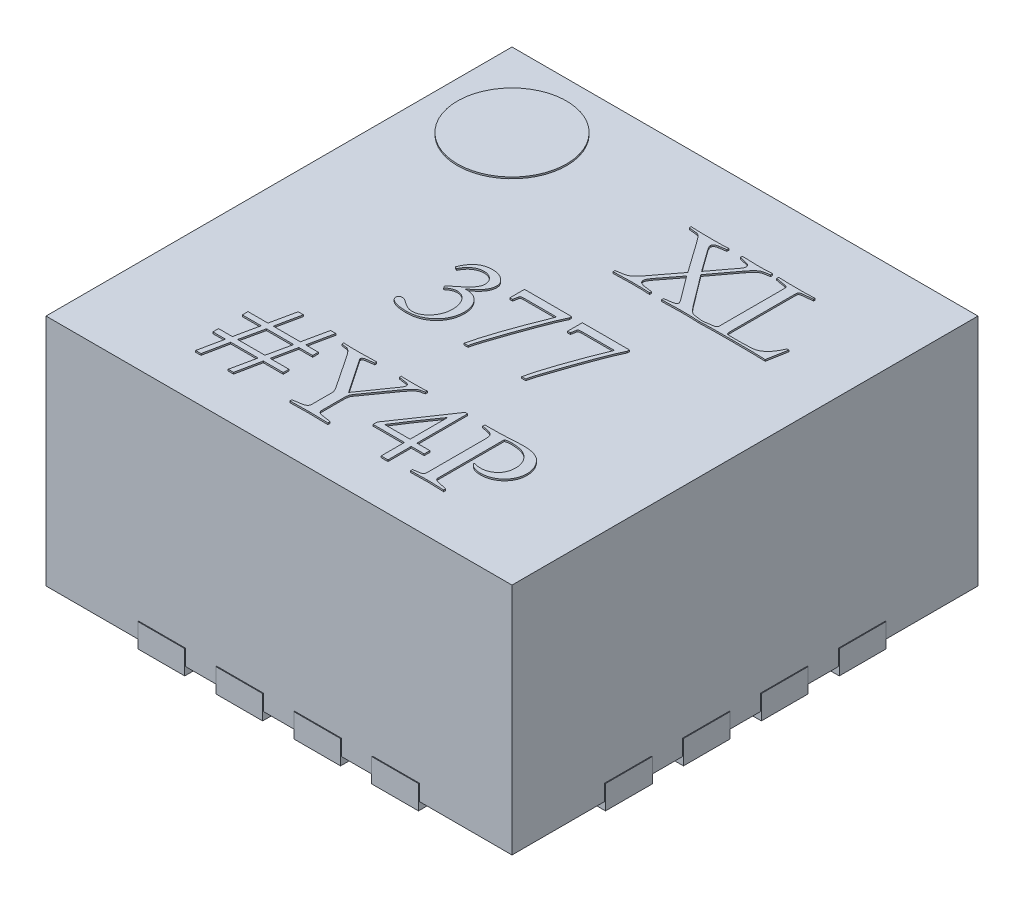
SolidWorks part; units mm, degrees
ref_plane "前视基准面" through (0, 0, 0) normal (0, 0, 1) x (1, 0, 0)
ref_plane "上视基准面" through (0, 0, 0) normal (0, 1, 0) x (1, 0, 0)
ref_plane "右视基准面" through (0, 0, 0) normal (1, 0, 0) x (0, 0, -1)
sketch "俯视" plane through (0, 0, 0) normal (0, 1, 0) x (1, 0, 0)
  line L1 (-1.495, 1.495) -> (1.495, 1.495)
  line L2 (-1.495, 1.495) -> (-1.495, -1.495)
  line L3 (-1.495, -1.495) -> (1.495, -1.495)
  line L4 (1.495, 1.495) -> (1.495, -1.495)
  line L5 (-1.495, 1.495) -> (1.495, -1.495) construction
  line L6 (-1.495, -1.495) -> (1.495, 1.495) construction
  point P0 (0, 0)
  dimension "D1" = 2.99
  dimension "D2" = 1.495
extrude "凸台-拉伸1" add sketch "俯视" against normal blind 1.5
ref_plane "基准面1" through (0, -1.55, 0) normal (0, 1, 0) x (1, 0, 0)
sketch "焊盘视图" plane through (0, -1.55, 0) normal (0, 1, 0) x (1, 0, 0)
  line L0 (0, 2) -> (0, -2) construction
  line L1 (-2, 0) -> (2, 0) construction
  line L2 (-1.5, 1.5) -> (1.5, 1.5) construction
  line L3 (-1.5, 1.5) -> (-1.5, -1.5) construction
  line L4 (-1.5, -1.5) -> (1.5, -1.5) construction
  line L5 (1.5, -1.5) -> (1.5, 1.5) construction
  line L6 (0.1, 1.5) -> (0.1, 1.25)
  line L7 (0.25, 2) -> (0.25, 1.3) construction
  line L8 (0.4, 1.5) -> (0.4, 1.25)
  line L10 (-0.25, 2) -> (-0.25, 1.3) construction
  line L11 (-0.75, 2) -> (-0.75, 1.3) construction
  line L12 (-2, -0.25) -> (-1.1693, -0.25) construction
  line L13 (-2, -0.75) -> (-1.1693, -0.75) construction
  line L14 (-2, 0.25) -> (-1.1693, 0.25) construction
  line L15 (-2, 0.75) -> (-1.1693, 0.75) construction
  line L16 (0.25, -2) -> (0.25, -1.1582) construction
  line L17 (-0.25, -2) -> (-0.25, -1.1275) construction
  line L18 (0.75, -2) -> (0.75, -1.1582) construction
  line L19 (-0.75, -2) -> (-0.75, -1.1275) construction
  line L20 (1.118, -0.75) -> (2, -0.75) construction
  line L21 (1.118, -0.25) -> (2, -0.25) construction
  line L22 (1.118, 0.25) -> (2, 0.25) construction
  line L23 (1.118, 0.75) -> (2, 0.75) construction
  line L24 (0.75, 1.3) -> (0.75, 2) construction
  line L25 (0.4, 1.5) -> (0.1, 1.5)
  line L26 (-0.4, 1.5) -> (-0.4, 1.25)
  line L27 (-0.1, 1.5) -> (-0.1, 1.25)
  line L28 (-0.1, 1.5) -> (-0.4, 1.5)
  line L29 (-0.6, -1.5) -> (-0.6, -1.25)
  line L30 (-0.9, -1.5) -> (-0.9, -1.25)
  line L31 (-0.9, -1.5) -> (-0.6, -1.5)
  line L32 (-0.9, 1.5) -> (-0.9, 1.25)
  line L33 (-0.6, 1.5) -> (-0.6, 1.25)
  line L34 (-0.6, 1.5) -> (-0.9, 1.5)
  line L35 (-1.5, -0.9) -> (-1.25, -0.9)
  line L36 (-1.5, -0.6) -> (-1.25, -0.6)
  line L37 (-1.5, -0.6) -> (-1.5, -0.9)
  line L38 (0.4, -1.5) -> (0.4, -1.25)
  line L39 (0.1, -1.5) -> (0.1, -1.25)
  line L40 (0.1, -1.5) -> (0.4, -1.5)
  line L41 (0.9, -1.5) -> (0.9, -1.25)
  line L42 (0.6, -1.5) -> (0.6, -1.25)
  line L43 (0.6, -1.5) -> (0.9, -1.5)
  line L44 (-1.5, 0.6) -> (-1.25, 0.6)
  line L45 (-1.5, 0.9) -> (-1.25, 0.9)
  line L46 (-1.5, 0.9) -> (-1.5, 0.6)
  line L47 (-0.1, -1.5) -> (-0.1, -1.25)
  line L48 (-0.4, -1.5) -> (-0.4, -1.25)
  line L49 (-0.4, -1.5) -> (-0.1, -1.5)
  line L50 (-1.5, -0.4) -> (-1.25, -0.4)
  line L51 (-1.5, -0.1) -> (-1.25, -0.1)
  line L52 (-1.5, -0.1) -> (-1.5, -0.4)
  line L53 (-1.5, 0.1) -> (-1.25, 0.1)
  line L54 (-1.5, 0.4) -> (-1.25, 0.4)
  line L55 (-1.5, 0.4) -> (-1.5, 0.1)
  line L56 (1.5, -0.6) -> (1.25, -0.6)
  line L57 (1.5, -0.9) -> (1.25, -0.9)
  line L58 (1.5, -0.9) -> (1.5, -0.6)
  line L59 (1.5, -0.1) -> (1.25, -0.1)
  line L60 (1.5, -0.4) -> (1.25, -0.4)
  line L61 (1.5, -0.4) -> (1.5, -0.1)
  line L62 (1.5, 0.4) -> (1.25, 0.4)
  line L63 (1.5, 0.1) -> (1.25, 0.1)
  line L64 (1.5, 0.1) -> (1.5, 0.4)
  line L65 (1.5, 0.9) -> (1.25, 0.9)
  line L66 (1.5, 0.6) -> (1.25, 0.6)
  line L67 (1.5, 0.6) -> (1.5, 0.9)
  line L68 (0.6, 1.5) -> (0.6, 1.25)
  line L69 (0.9, 1.5) -> (0.9, 1.25)
  line L70 (0.9, 1.5) -> (0.6, 1.5)
  arc A0 (0.1, 1.25) -> (0.4, 1.25) centre (0.25, 1.25) ccw
  arc A1 (-0.4, 1.25) -> (-0.1, 1.25) centre (-0.25, 1.25) ccw
  arc A2 (-0.6, -1.25) -> (-0.9, -1.25) centre (-0.75, -1.25) ccw
  arc A3 (-0.9, 1.25) -> (-0.6, 1.25) centre (-0.75, 1.25) ccw
  arc A4 (-1.25, -0.9) -> (-1.25, -0.6) centre (-1.25, -0.75) ccw
  arc A5 (0.4, -1.25) -> (0.1, -1.25) centre (0.25, -1.25) ccw
  arc A6 (0.9, -1.25) -> (0.6, -1.25) centre (0.75, -1.25) ccw
  arc A7 (-1.25, 0.6) -> (-1.25, 0.9) centre (-1.25, 0.75) ccw
  arc A8 (-0.1, -1.25) -> (-0.4, -1.25) centre (-0.25, -1.25) ccw
  arc A9 (-1.25, -0.4) -> (-1.25, -0.1) centre (-1.25, -0.25) ccw
  arc A10 (-1.25, 0.1) -> (-1.25, 0.4) centre (-1.25, 0.25) ccw
  arc A11 (1.25, -0.6) -> (1.25, -0.9) centre (1.25, -0.75) ccw
  arc A12 (1.25, -0.1) -> (1.25, -0.4) centre (1.25, -0.25) ccw
  arc A13 (1.25, 0.4) -> (1.25, 0.1) centre (1.25, 0.25) ccw
  arc A14 (1.25, 0.9) -> (1.25, 0.6) centre (1.25, 0.75) ccw
  arc A15 (0.6, 1.25) -> (0.9, 1.25) centre (0.75, 1.25) ccw
  dimension "D18" = 0.15
  dimension "D1" = 0.3
  dimension "D2" = 0.3
  dimension "D3" = 0.3
  dimension "D4" = 0.3
  dimension "D5" = 0.3
  dimension "D6" = 0.3
  dimension "D7" = 0.3
  dimension "D8" = 0.3
  dimension "D9" = 0.3
  dimension "D10" = 0.3
  dimension "D11" = 0.3
  dimension "D12" = 0.3
  dimension "D13" = 0.3
  dimension "D14" = 0.3
  dimension "D15" = 0.3
  dimension "D16" = 0.3
  dimension "D17" = 0.25
  dimension "D19" = 1.5
  dimension "D20" = 0.5
  dimension "D21" = 3
  dimension "D22" = 3
extrude "凸台-拉伸2" add sketch "焊盘视图" along normal blind 0.152 separate body
sketch "型号" plane through (0, 0, 0) normal (0, 1, 0) x (1, 0, 0)
  text T0 "     XL\r\n  377\r\n#Y4P" font "华文宋体" height 0.5
extrude "凸台-拉伸6" add sketch "型号" along normal blind 0.01
ref_plane "基准面2" through (0, 0.01, 0) normal (0, 1, 0) x (1, 0, 0)
sketch "草图3" plane through (0, 0.01, 0) normal (0, 1, 0) x (1, 0, 0)
  circle A0 centre (-1, 1) radius 0.35
extrude "凸台-拉伸7" add sketch "草图3" along normal blind 0.01 separate body
